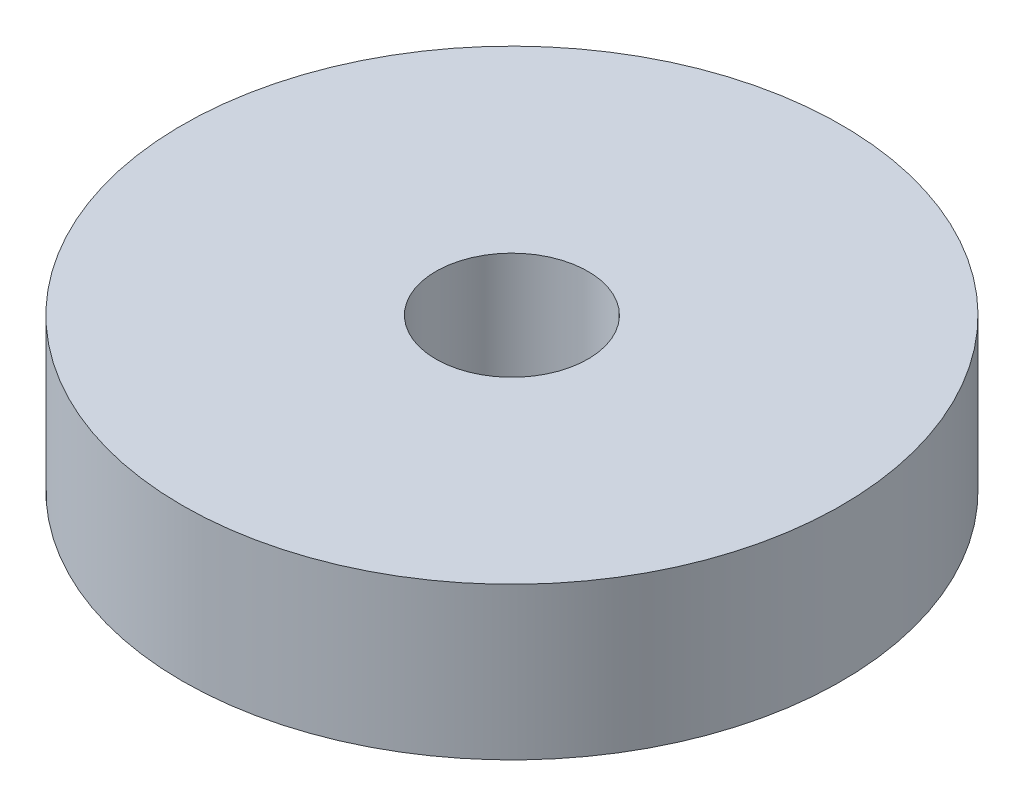
SolidWorks part; units mm, degrees
ref_plane "前视基准面" through (0, 0, 0) normal (0, 0, 1) x (1, 0, 0)
ref_plane "上视基准面" through (0, 0, 0) normal (0, 1, 0) x (1, 0, 0)
ref_plane "右视基准面" through (0, 0, 0) normal (1, 0, 0) x (0, 0, -1)
other "Configuration Table"
sketch "草图1" plane through (0, 0, 0) normal (0, 1, 0) x (1, 0, 0)
  circle A0 centre (0, 0) radius 6.5
  circle A1 centre (0, 0) radius 1.5
  dimension "D1" = 13
  dimension "D2" = 3
extrude "凸台-拉伸1" add sketch "草图1" along normal blind 3
